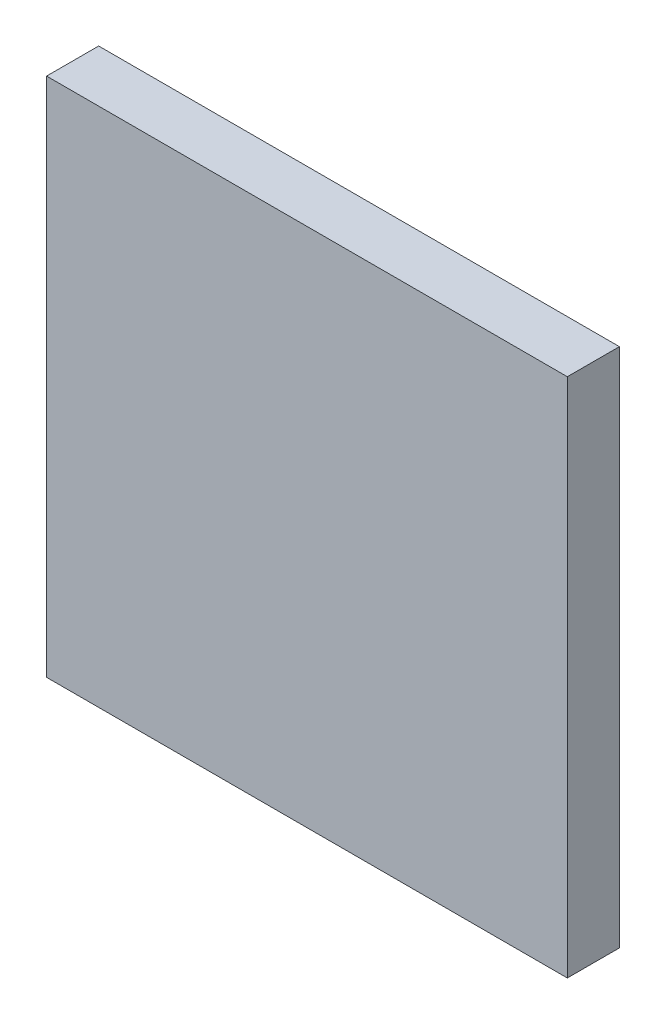
SolidWorks part; units mm, degrees
ref_plane "Front Plane" through (0, 0, 0) normal (0, 0, 1) x (1, 0, 0)
ref_plane "Top Plane" through (0, 0, 0) normal (0, 1, 0) x (1, 0, 0)
ref_plane "Right Plane" through (0, 0, 0) normal (1, 0, 0) x (0, 0, -1)
sketch "Sketch1" plane through (0, 0, 0) normal (0, 0, 1) x (1, 0, 0)
  line L1 (-50, -50) -> (50, -50)
  line L2 (-50, -50) -> (-50, 50)
  line L3 (-50, 50) -> (50, 50)
  line L4 (50, -50) -> (50, 50)
  line L5 (-50, -50) -> (50, 50) construction
  line L6 (-50, 50) -> (50, -50) construction
  point P0 (0, 0)
  dimension "D1" = 100
  dimension "D2" = 100
extrude "Boss-Extrude1" add sketch "Sketch1" along normal blind 10
